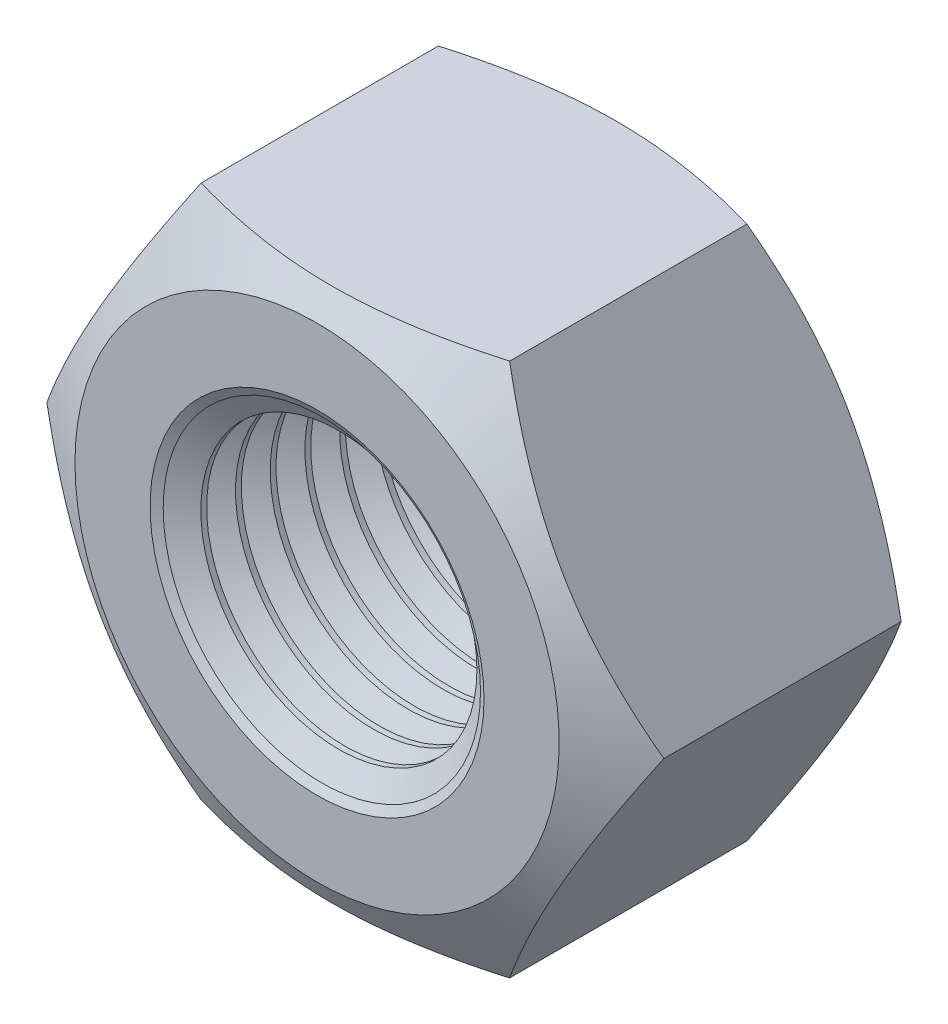
SolidWorks part; units mm, degrees
ref_plane "Front" through (0, 0, 0) normal (0, 0, 1) x (1, 0, 0)
ref_plane "Top" through (0, 0, 0) normal (0, 1, 0) x (1, 0, 0)
ref_plane "Right" through (0, 0, 0) normal (1, 0, 0) x (0, 0, -1)
sketch "Sketch1" plane through (0, 0, 0) normal (0, 0, 1) x (1, 0, 0)
  line L1 (4.6188, 0) -> (2.3094, 4)
  line L2 (2.3094, 4) -> (-2.3094, 4)
  line L3 (-2.3094, 4) -> (-4.6188, 0)
  line L4 (-4.6188, 0) -> (-2.3094, -4)
  line L5 (-2.3094, -4) -> (2.3094, -4)
  line L6 (2.3094, -4) -> (4.6188, 0)
  circle A0 centre (0, 0) radius 4 construction
  circle A1 centre (0, 0) radius 2.067
  dimension "D" = 4.134
  dimension "s" = 8
extrude "BaseNut" add sketch "Sketch1" against normal blind 4.7
cosmetic thread "ThreadCosmetic1" [suppressed] parameters "D"=5
sketch "Sketch2" plane through (0, 0, 0) normal (0, 1, 0) x (1, 0, 0)
  line L0 (-4.6188, 4.7) -> (-3.625, 4.7)
  line L2 (-3.625, 4.7) -> (-4.6188, 4.1262)
  line L3 (-4.6188, 4.1262) -> (-4.6188, 4.7)
  line L4 (0, 3.3759) -> (0, -9.8171) construction
  line L6 (-9.7712, 2.35) -> (9.8853, 2.35) construction
  line L7 (-4.6188, 0.5738) -> (-4.6188, 0)
  line L8 (-3.625, 0) -> (-4.6188, 0.5738)
  line L9 (-4.6188, 0) -> (-3.625, 0)
  dimension "dw" = 7.25
  dimension "D1" = 30
  dimension "D2" = 2.35
revolve "Double-Chamfer" cut sketch "Sketch2" angle 360 about L4
chamfer "EndChamfer" distance 0.433 angle 30 2 edges at (2.067, 0, -4.7) (2.067, 0, 0)
sketch "Sketch3" plane through (0, 0, 0) normal (0, 1, 0) x (1, 0, 0)
  line L0 (-2.442, 4.267) -> (-2.067, 4.0505)
  line L1 (-2.067, 4.0505) -> (-1.634, 4.0505)
  line L2 (-1.634, 4.0505) -> (-1.634, 4.4835)
  line L3 (-1.634, 4.4835) -> (-2.067, 4.4835)
  line L4 (-2.067, 4.4835) -> (-2.442, 4.267)
  line L5 (0, 7.4383) -> (0, 16.8806) construction
  dimension "D1" = 0.433
  dimension "D2" = 4.134
revolve "Cut-Revolve10" cut sketch "Sketch3" angle 360 about L5
pattern_linear "LPattern10" count 9 spacing 0.5196 along (0, 0, 1) of "Cut-Revolve10"
equation "\"dw@Sketch2\" = \"s@Sketch1\"-0.75"
equation "\"D2@Sketch2\" = \"m@BaseNut\" / 2"
equation "\"D2@Sketch3\" = \"D@Sketch1\""
equation "\"D1@Sketch3\" =  (\"D@ThreadCosmetic1\"   - \"D@Sketch1\")  / 2"
equation "\"D3@LPattern10\" = \"D1@Sketch3\" * 1.2"
equation "\"D1@LPattern10\" = \"m@BaseNut\"/\"D3@LPattern10\""
